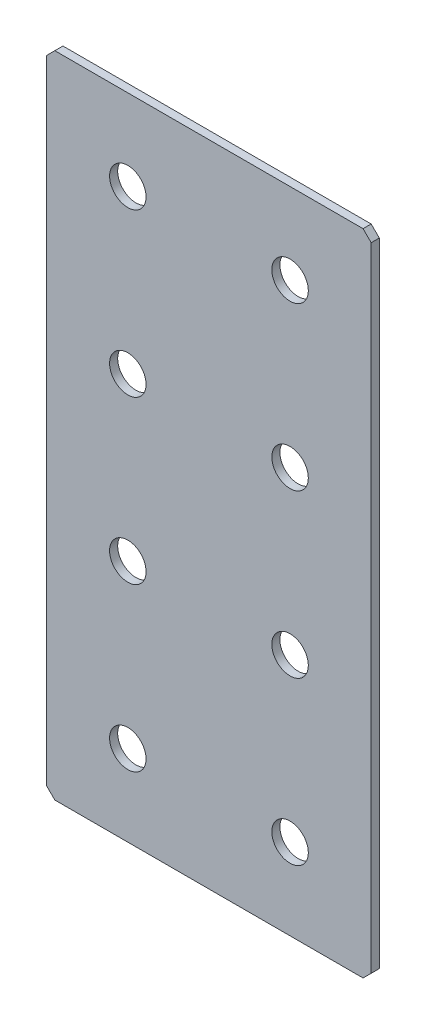
SolidWorks part; units mm, degrees
material "Простая углеродистая сталь"
ref_plane "Спереди(Плоскость XY)" through (0, 0, 0) normal (0, 0, 1) x (1, 0, 0)
ref_plane "Сверху(Плоскость XZ)" through (0, 0, 0) normal (0, 1, 0) x (1, 0, 0)
ref_plane "Справа(Плоскость ZY)" through (0, 0, 0) normal (1, 0, 0) x (0, 0, -1)
sketch "Эскиз1" plane through (0, 0, 0) normal (0, 0, 1) x (1, 0, 0)
  line L1 (-40, -80) -> (40, -80)
  line L2 (-40, -80) -> (-40, 80)
  line L3 (-40, 80) -> (40, 80)
  line L4 (40, -80) -> (40, 80)
  line L5 (-40, -80) -> (40, 80) construction
  line L6 (-40, 80) -> (40, -80) construction
  point P0 (0, 0)
  dimension "D1" = 80
  dimension "D2" = 160
extrude "Бобышка-Вытянуть1" add sketch "Эскиз1" along normal blind 2
chamfer "Фаска1" distance 2 angle 45 4 edges at (-40, -80, 1) (40, -80, 1) (-40, 80, 1) (40, 80, 1)
hole_wizard "Отверстие с зазором M81" positions "Эскиз2" profile "Эскиз3" hole size "M8" standard "DIN" end condition through all
sketch "Эскиз2" plane through (0, 0, 2) normal (0, 0, 1) x (1, 0, 0)
  line L2 (-20, 20) -> (20, 20) construction
  line L3 (-20, 20) -> (-20, 60) construction
  line L4 (-20, 60) -> (20, 60) construction
  line L5 (20, 20) -> (20, 60) construction
  line L7 (-20, -20) -> (20, -20) construction
  line L8 (-20, -20) -> (-20, -60) construction
  line L9 (-20, -60) -> (20, -60) construction
  line L10 (20, -20) -> (20, -60) construction
  line L11 (0, 20) -> (0, -20) construction
  point P0 (-20, 20)
  point P2 (20, 20)
  point P8 (-20, -20)
  point P10 (20, -20)
  point P22 (-20, 60)
  point P24 (20, 60)
  point P93 (20, -60)
  point P170 (-20, -60)
  dimension "D1" = 40
sketch "Эскиз3" plane through (-20, 20, 2) normal (1, 0, 0) x (0, -1, 0)
  line L0 (0, 0) -> (0, 2)
  line L1 (0, 2) -> (4.5, 2)
  line L2 (4.5, 2) -> (4.5, 0)
  line L5 (4.5, 0) -> (0, 0)
  line L11 (0, -6.35) -> (0, 107.95) construction
  dimension "Диаметр сквозного отверстия" = 9
  dimension "Глубина сквозного отверстия" = 2
